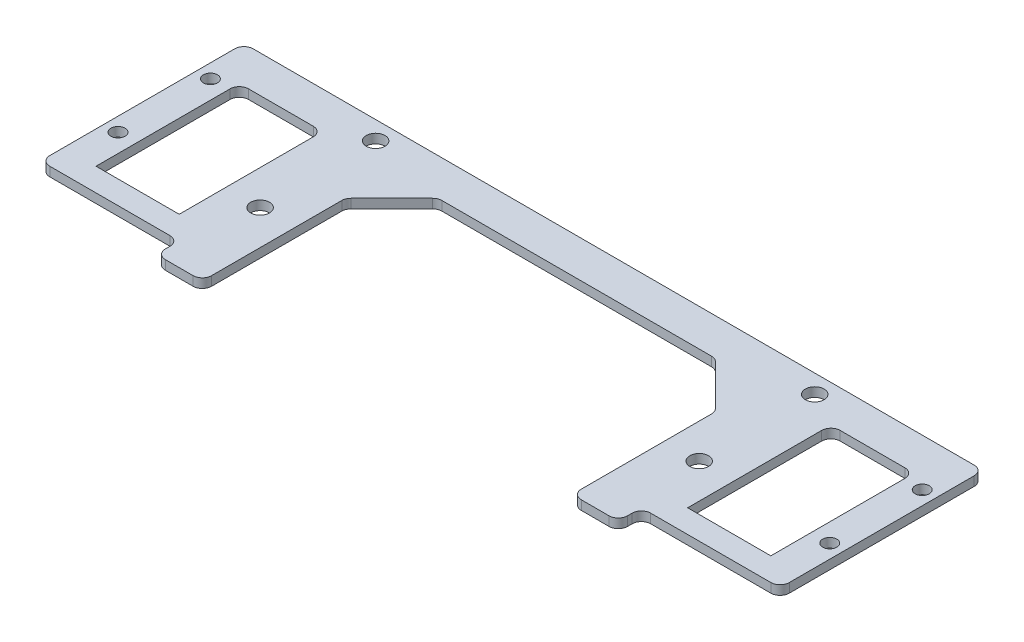
SolidWorks part; units mm, degrees
material "Thornel Mat VMA"
ref_plane "前视基准面" through (0, 0, 0) normal (0, 0, 1) x (1, 0, 0)
ref_plane "上视基准面" through (0, 0, 0) normal (0, 1, 0) x (1, 0, 0)
ref_plane "右视基准面" through (0, 0, 0) normal (1, 0, 0) x (0, 0, -1)
other "Configuration Table"
sketch "草图1" plane through (0, 0, 0) normal (0, 1, 0) x (1, 0, 0)
  line L0 (0, 0) -> (0, -50000) construction
  line L1 (-47.5, 12.5) -> (47.5, 12.5) construction
  line L2 (-47.5, 12.5) -> (-47.5, -12.5) construction
  line L3 (-47.5, -12.5) -> (47.5, -12.5) construction
  line L4 (47.5, 12.5) -> (47.5, -12.5) construction
  line L5 (-47.5, 12.5) -> (47.5, -12.5) construction
  line L6 (-47.5, -12.5) -> (47.5, 12.5) construction
  line L8 (-80, -32.5) -> (80, -32.5)
  line L9 (-80, -32.5) -> (-80, 16.5)
  line L10 (-80, 16.5) -> (80, 16.5)
  line L11 (80, -32.5) -> (80, 16.5)
  line L12 (-80, -32.5) -> (80, 16.5) construction
  line L13 (-80, 16.5) -> (80, -32.5) construction
  line L14 (-77, -13.75) -> (77, -13.75) construction
  line L15 (-77, -13.75) -> (-77, 6.25) construction
  line L16 (-77, 6.25) -> (77, 6.25) construction
  line L17 (77, -13.75) -> (77, 6.25) construction
  line L18 (-77, -13.75) -> (77, 6.25) construction
  line L19 (-77, 6.25) -> (77, -13.75) construction
  circle A0 centre (-77, -13.75) radius 1.525
  circle A1 centre (-77, 6.25) radius 1.525
  circle A2 centre (77, 6.25) radius 1.525
  circle A3 centre (77, -13.75) radius 1.525
  circle A4 centre (-47.5, 12.5) radius 2.025
  circle A5 centre (-47.5, -12.5) radius 2.025
  circle A6 centre (47.5, 12.5) radius 2.025
  circle A7 centre (47.5, -12.5) radius 2.025
  point P0 (0, 0)
  point P8 (0, -8)
  point P14 (0, -3.75)
  dimension "D9" = 3.05
  dimension "D10" = 4.05
  dimension "D1" = 95
  dimension "D2" = 25
  dimension "D3" = 20
  dimension "D4" = 49
  dimension "D5" = 20
  dimension "D6" = 154
  dimension "D7" = 18.75
  dimension "D8" = 3
extrude "凸台-拉伸1" add sketch "草图1" along normal blind 2
sketch "草图2" plane through (0, 2, 0) normal (0, 1, 0) x (1, 0, 0)
  line L0 (-80, -8) -> (49920, -8) construction
  line L1 (-40, -24.5) -> (40, -24.5)
  line L2 (-40, -24.5) -> (-40, 8.5)
  line L3 (-40, 8.5) -> (40, 8.5)
  line L4 (40, -24.5) -> (40, 8.5)
  line L5 (-40, -24.5) -> (40, 8.5) construction
  line L6 (-40, 8.5) -> (40, -24.5) construction
  line L7 (-80, 16.5) -> (-80, -32.5) construction
  line L8 (0, 0) -> (0, -8) construction
  line L9 (80, 16.5) -> (-80, 16.5) construction
  line L10 (73, -24.5) -> (55, -24.5)
  line L11 (-73, 8.5) -> (-55, 8.5)
  line L12 (-73, 8.5) -> (-73, -24.5)
  line L13 (-73, -24.5) -> (-55, -24.5)
  line L14 (-55, 8.5) -> (-55, -24.5)
  line L15 (55, 8.5) -> (55, -24.5)
  line L16 (73, 8.5) -> (55, 8.5)
  line L17 (73, 8.5) -> (73, -24.5)
  circle A0 centre (-47.5, 12.5) radius 2.025 construction
  circle A1 centre (-77, 6.25) radius 1.525 construction
  point P0 (0, -8)
  point P9 (-80, -8)
  dimension "D2" = 7.5
  dimension "D3" = 7.5
  dimension "D4" = 4
  dimension "D1" = 8
extrude "切除-拉伸1" cut sketch "草图2" against normal blind 10
chamfer "倒角1" distance 10 angle 45 4 edges at (-40, 1, 24.5) (40, 1, 24.5) (40, 1, -8.5) (-40, 1, -8.5)
fillet "圆角1" radius 2 16 edges at (40, 1, 14.5) (30, 1, 24.5) (-30, 1, 24.5) (-40, 1, 14.5) (-40, 1, 1.5) (-30, 1, -8.5) (30, 1, -8.5) (40, 1, 1.5) (-73, 1, -8.5) (-55, 1, -8.5) (-55, 1, 24.5) (-73, 1, 24.5) (73, 1, 24.5) (55, 1, -8.5) (73, 1, -8.5) (55, 1, 24.5)
sketch "草图3" plane through (0, 0, 0) normal (0, -1, 0) x (1, 0, 0)
  line L0 (0, 0) -> (0, -50000) construction
  line L1 (-80, 27.5) -> (-50, 27.5)
  line L2 (-80, 27.5) -> (-80, 32.5)
  line L3 (-80, 32.5) -> (-50, 32.5)
  line L4 (-50, 27.5) -> (-50, 32.5)
  line L5 (50, 27.5) -> (50, 32.5)
  line L6 (80, 32.5) -> (50, 32.5)
  line L7 (80, 27.5) -> (80, 32.5)
  line L8 (80, 27.5) -> (50, 27.5)
  dimension "D1" = 30
  dimension "D2" = 5
extrude "切除-拉伸2" cut sketch "草图3" against normal blind 10
sketch "草图4" plane through (0, 0, 0) normal (0, -1, 0) x (1, 0, 0)
  line L0 (-55, -6.5) -> (-55, 22.5) construction
  line L1 (-80, 27.5) -> (-55, 27.5)
  line L2 (-80, 27.5) -> (-80, 22.5)
  line L3 (-80, 22.5) -> (-55, 22.5)
  line L4 (-55, 27.5) -> (-55, 22.5)
  line L5 (55, 22.5) -> (55, -6.5) construction
  line L6 (80, 27.5) -> (55, 27.5)
  line L7 (80, 27.5) -> (80, 22.5)
  line L8 (80, 22.5) -> (55, 22.5)
  line L9 (55, 27.5) -> (55, 22.5)
  dimension "D1" = 5
extrude "凸台-拉伸2" add sketch "草图4" against normal up to surface (2 mm away) up to face at (64, 2, 8)
fillet "圆角2" radius 2 8 edges at (80, 1, 27.5) (50, 1, 27.5) (50, 1, 32.5) (-50, 1, 27.5) (-80, 1, 27.5) (-80, 1, -16.5) (80, 1, -16.5) (-50, 1, 32.5)
sketch "草图5" plane through (0, 0, 0) normal (0, -1, 0) x (1, 0, 0)
  line L0 (-48, 32.5) -> (48, 32.5) construction
  line L1 (-40, 13.6716) -> (40, 13.6716)
  line L2 (-40, 13.6716) -> (-40, 32.5)
  line L3 (-40, 32.5) -> (40, 32.5)
  line L4 (40, 13.6716) -> (40, 32.5)
  point P5 (40, 16.6716)
  point P7 (0, 0)
extrude "切除-拉伸3" cut sketch "草图5" against normal blind 10
fillet "圆角3" radius 2 2 edges at (40, 1, 32.5) (-40, 1, 32.5)
